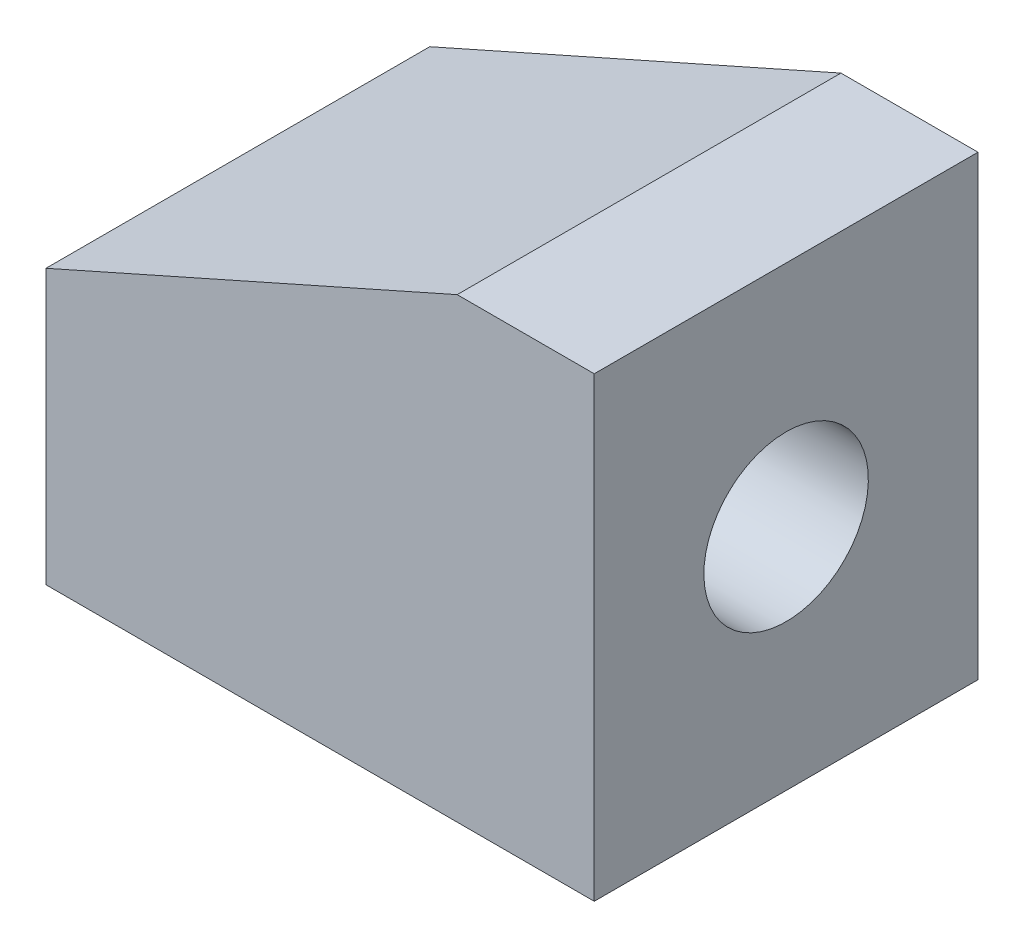
SolidWorks part; units mm, degrees
ref_plane "Front Plane" through (0, 0, 0) normal (0, 0, 1) x (1, 0, 0)
ref_plane "Top Plane" through (0, 0, 0) normal (0, 1, 0) x (1, 0, 0)
ref_plane "Right Plane" through (0, 0, 0) normal (1, 0, 0) x (0, 0, -1)
sketch "Sketch1" plane through (0, 0, 0) normal (0, 0, 1) x (1, 0, 0)
  line L0 (-38.2353, -17.0588) -> (21.7647, -17.0588)
  line L1 (21.7647, -17.0588) -> (21.7647, 32.9412)
  line L4 (-38.2353, 12.9412) -> (-38.2353, -17.0588)
  line L5 (21.7647, 32.9412) -> (6.7647, 32.9412)
  line L6 (6.7647, 32.9412) -> (-38.2353, 12.9412)
  dimension "D1" = 30
  dimension "D2" = 60
  dimension "D3" = 50
  dimension "D4" = 15
extrude "Boss-Extrude1" add sketch "Sketch1" along normal blind 42
sketch "Sketch2" plane through (21.7647, 0, 0) normal (1, 0, 0) x (0, 0, -1)
  line L0 (0, -17.0588) -> (0, 32.9412) construction
  line L1 (-42, -17.0588) -> (0, -17.0588) construction
  circle A0 centre (-21, 7.9412) radius 9
  point P2 (0, 0)
  point P5 (0, 0)
  point P6 (0, 7.9412)
  point P9 (-21, -17.0588)
  dimension "D1" = 18
extrude "Cut-Extrude1" cut sketch "Sketch2" against normal blind 40
